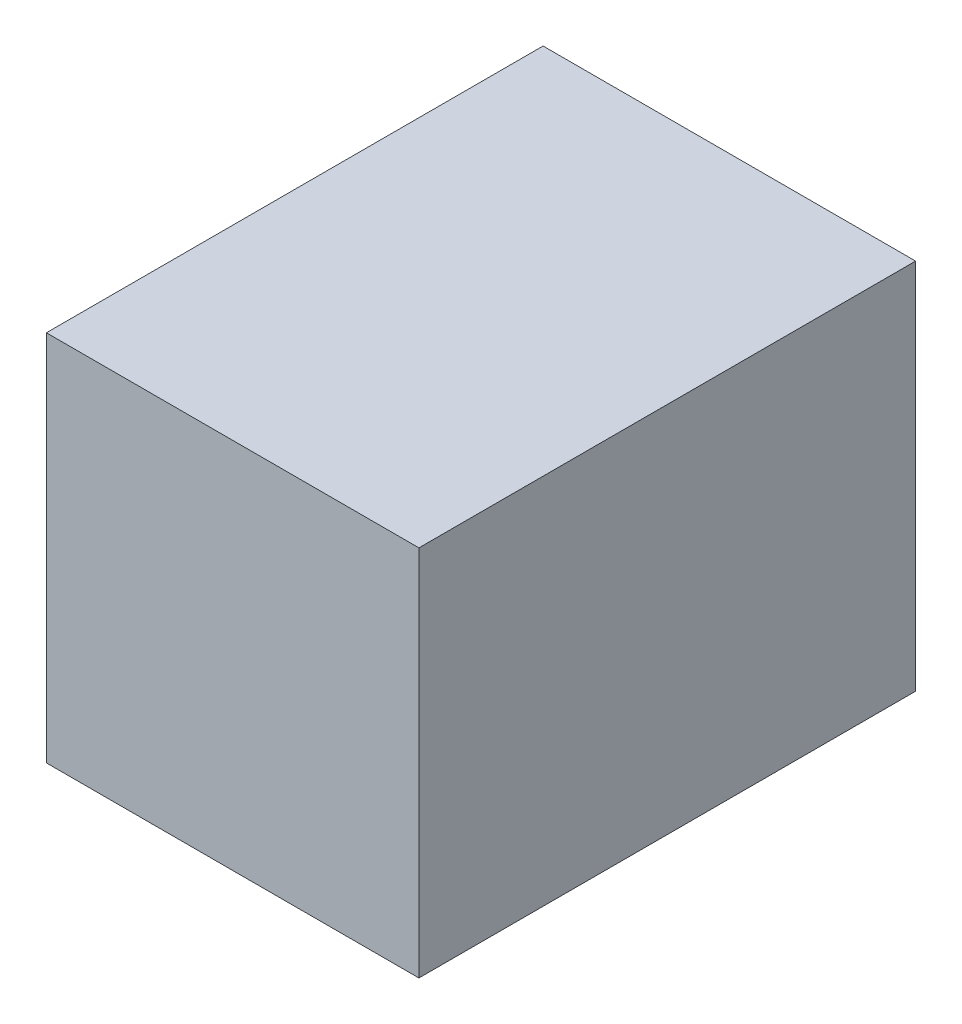
SolidWorks part; units mm, degrees
ref_plane "前视基准面" through (0, 0, 0) normal (0, 0, 1) x (1, 0, 0)
ref_plane "上视基准面" through (0, 0, 0) normal (0, 1, 0) x (1, 0, 0)
ref_plane "右视基准面" through (0, 0, 0) normal (1, 0, 0) x (0, 0, -1)
sketch "草图1" plane through (0, 0, 0) normal (0, 0, 1) x (1, 0, 0)
  line L1 (-7.5, 7.5) -> (7.5, 7.5)
  line L2 (-7.5, 7.5) -> (-7.5, -7.5)
  line L3 (-7.5, -7.5) -> (7.5, -7.5)
  line L4 (7.5, 7.5) -> (7.5, -7.5)
  line L5 (-7.5, 7.5) -> (7.5, -7.5) construction
  line L6 (-7.5, -7.5) -> (7.5, 7.5) construction
  point P0 (0, 0)
  dimension "D1" = 15
  dimension "D2" = 15
extrude "凸台-拉伸1" add sketch "草图1" along normal blind 20
sketch "草图2" plane through (0, 0, 0) normal (0, 0, 1) x (1, 0, 0)
  line L1 (6, 6) -> (-6, 6)
  line L2 (6, 6) -> (6, -6)
  line L3 (6, -6) -> (-6, -6)
  line L4 (-6, 6) -> (-6, -6)
  line L5 (6, 6) -> (-6, -6) construction
  line L6 (6, -6) -> (-6, 6) construction
  point P0 (0, 0)
  dimension "D1" = 12
  dimension "D2" = 12
extrude "切除-拉伸1" cut sketch "草图2" against normal blind 0.001 and the other way blind 17
